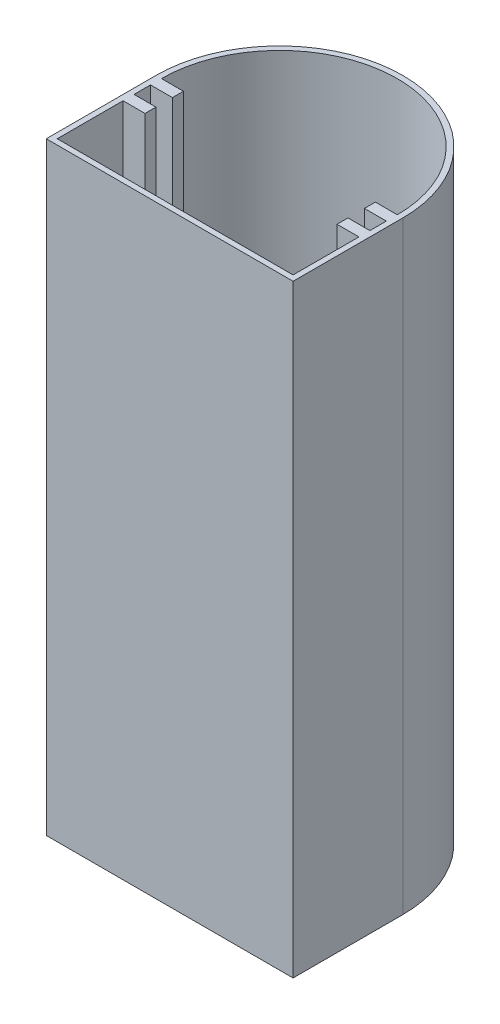
SolidWorks part; units mm, degrees
ref_plane "Front Plane" through (0, 0, 0) normal (0, 0, 1) x (1, 0, 0)
ref_plane "Top Plane" through (0, 0, 0) normal (0, 1, 0) x (1, 0, 0)
ref_plane "Right Plane" through (0, 0, 0) normal (1, 0, 0) x (0, 0, -1)
sketch "Sketch1" plane through (0, 0, 0) normal (0, 1, 0) x (1, 0, 0)
  line L0 (-43.8831, -1.7077) -> (1.1169, -1.7077)
  line L2 (-43.8831, -1.7077) -> (-43.8831, 18.2923)
  line L4 (1.1169, -1.7077) -> (1.1169, 18.2923)
  arc A0 (1.1169, 18.2923) -> (-43.8831, 18.2923) centre (-21.3831, 18.2923) ccw
  dimension "D3" = 22.5
  dimension "D1" = 45
  dimension "D2" = 20
extrude "Boss-Extrude1" add sketch "Sketch1" along normal blind 110 contours L2 A0 L4 L0
sketch "Sketch2" plane through (0, 110, 0) normal (0, 1, 0) x (1, 0, 0)
  line L5 (-42.8831, 16.2923) -> (-42.8831, 13.2923)
  line L6 (-42.8831, -0.7077) -> (0.1169, -0.7077)
  line L8 (-42.8831, 18.2923) -> (-38.8831, 18.2923)
  line L9 (-38.8831, 18.2923) -> (-38.8831, 16.2923)
  line L10 (-38.8831, 16.2923) -> (-42.8831, 16.2923)
  line L12 (-42.8831, 13.2923) -> (-38.8831, 13.2923)
  line L13 (-38.8831, 13.2923) -> (-38.8831, 11.2923)
  line L14 (-38.8831, 11.2923) -> (-42.8831, 11.2923)
  line L15 (0.1169, 11.2923) -> (0.1169, -0.7077)
  line L16 (-42.8831, 11.2923) -> (-42.8831, -0.7077)
  line L17 (-3.8831, 11.2923) -> (0.1169, 11.2923)
  line L18 (-3.8831, 13.2923) -> (-3.8831, 11.2923)
  line L19 (0.1169, 13.2923) -> (-3.8831, 13.2923)
  line L20 (-3.8831, 16.2923) -> (0.1169, 16.2923)
  line L21 (-3.8831, 18.2923) -> (-3.8831, 16.2923)
  line L22 (0.1169, 18.2923) -> (-3.8831, 18.2923)
  line L23 (-43.8831, -1.7077) -> (1.1169, -1.7077) construction
  line L24 (-43.8831, -1.7077) -> (-43.8831, 18.2923) construction
  line L25 (0.1169, 16.2923) -> (0.1169, 13.2923)
  arc A4 (0.1169, 18.2923) -> (-42.8831, 18.2923) centre (-21.3831, 18.2923) ccw
  point P7 (0, 0)
  point P8 (0, 0)
  point P25 (-21.3831, -0.7077)
  point P26 (0, 0)
  dimension "D1" = 4
  dimension "D2" = 2
  dimension "D3" = 3
  dimension "D4" = 2
  dimension "D5" = 4
  dimension "D6" = 1
  dimension "D7" = 1
  dimension "D8" = 4
  dimension "D9" = 3
  dimension "D10" = 2
  dimension "D11" = 2
  dimension "D12" = 1
extrude "Cut-Extrude1" cut sketch "Sketch2" against normal blind 109
sketch "Sketch3" plane through (-43.8831, 0, 0) normal (-1, 0, 0) x (0, 0, 1)
  line L0 (1.7077, 110) -> (1.7077, 0) construction
  line L1 (1.7077, 110) -> (-18.2923, 110) construction
  circle A0 centre (-4.9589, 55) radius 2.875
  point P4 (0, 0)
  dimension "D1" = 5.75
  dimension "D2" = 6.6667
  dimension "D3" = 55
extrude "Cut-Extrude2" cut sketch "Sketch3" against normal blind 5
equation "\"Width\"= 45"
equation "\"Depth\"= 20"
equation "\"lenght\"= 110"
equation "\"thick\"= 1"
equation "\"D1@Sketch1\"=\"Width\""
equation "\"D3@Sketch1\"=\"Width\"/2"
equation "\"length\"= 110"
equation "\"D1@Boss-Extrude1\"=\"length\""
equation "\"holder lenght\"= 4"
equation "\"holder width\"= 2"
equation "\"holder gap\"= 3"
equation "\"D1@Sketch2\"=\"holder lenght\""
equation "\"D2@Sketch2\"=\"holder width\""
equation "\"D3@Sketch2\"=\"holder gap\""
equation "\"D4@Sketch2\"=\"holder width\""
equation "\"D5@Sketch2\"=\"holder lenght\""
equation "\"D6@Sketch2\"=\"thick\""
equation "\"D7@Sketch2\"=\"thick\""
equation "\"D1@Cut-Extrude1\"=\"length\"-\"thick\""
equation "\"fillet\"= 0.5"
equation "\"D2@Sketch1\"=\"Depth\""
equation "\"D8@Sketch2\"=\"holder lenght\""
equation "\"D9@Sketch2\"=\"holder gap\""
equation "\"D10@Sketch2\"=\"holder width\""
equation "\"D11@Sketch2\"=\"holder width\""
equation "\"hole\"=5.75"
equation "\"D1@Sketch3\"=\"hole\""
equation "\"D2@Sketch3\"=\"Depth\"/3"
equation "\"D3@Sketch3\"=\"lenght\"/2"
equation "\"D12@Sketch2\"=\"thick\""
